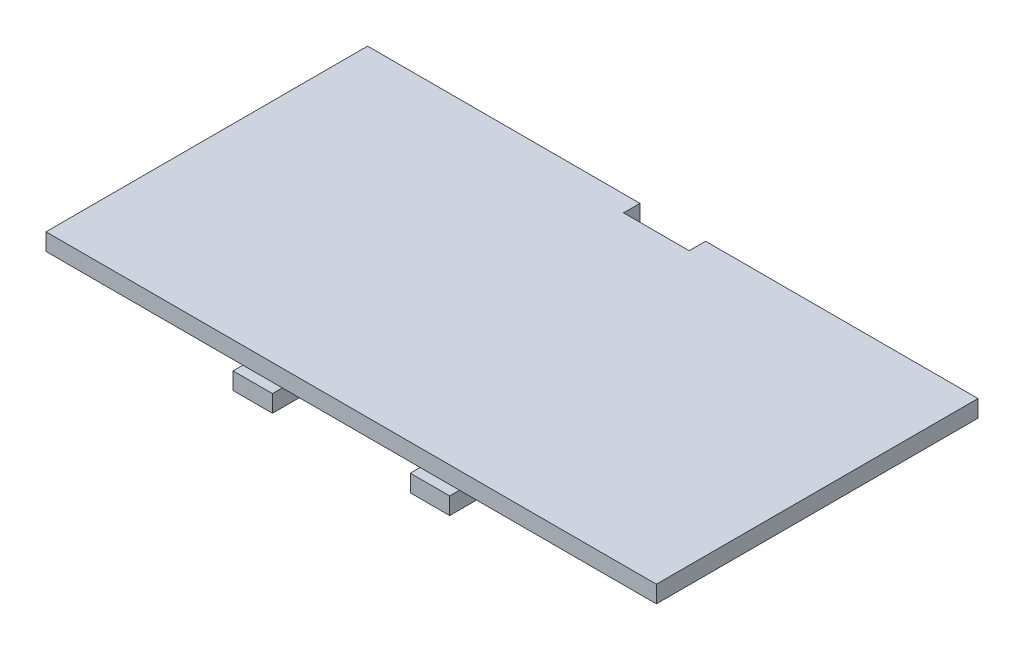
SolidWorks part; units mm, degrees
ref_plane "Front" through (0, 0, 0) normal (0, 0, 1) x (1, 0, 0)
ref_plane "Top" through (0, 0, 0) normal (0, 1, 0) x (1, 0, 0)
ref_plane "Right" through (0, 0, 0) normal (1, 0, 0) x (0, 0, -1)
sketch "Sketch1" plane through (0, 0, 0) normal (0, 1, 0) x (1, 0, 0)
  line L1 (-46.5, -24.5) -> (46.5, -24.5)
  line L2 (-46.5, -24.5) -> (-46.5, 24.5)
  line L3 (-46.5, 24.5) -> (46.5, 24.5)
  line L4 (46.5, -24.5) -> (46.5, 24.5)
  line L5 (-46.5, -24.5) -> (46.5, 24.5) construction
  line L6 (-46.5, 24.5) -> (46.5, -24.5) construction
  point P0 (0, 0)
  dimension "D1" = 49
  dimension "D2" = 93
extrude "Boss-Extrude1" add sketch "Sketch1" along normal blind 2.6
sketch "Sketch2" plane through (0, 2.6, 0) normal (0, 1, 0) x (1, 0, 0)
  line L0 (46.5, 24.5) -> (-46.5, 24.5) construction
  line L1 (-5, 24.5) -> (5, 24.5)
  line L2 (-5, 24.5) -> (-5, 22)
  line L3 (-5, 22) -> (5, 22)
  line L4 (5, 24.5) -> (5, 22)
  line L5 (-5, 24.5) -> (5, 22) construction
  line L6 (-5, 22) -> (5, 24.5) construction
  line L7 (0, 0) -> (0, 23.25) construction
  point P4 (0, 23.25)
  dimension "D1" = 2.5
  dimension "D2" = 10
extrude "Cut-Extrude1" cut sketch "Sketch2" against normal blind 2.6
sketch "Sketch3" plane through (0, 0, 0) normal (0, -1, 0) x (1, 0, 0)
  line L0 (-46.5, 24.5) -> (46.5, 24.5) construction
  line L1 (-16.5, 23) -> (-10.5, 23) construction
  line L2 (-16.5, 23) -> (-16.5, 26)
  line L3 (-16.5, 26) -> (-10.5, 26)
  line L4 (-10.5, 23) -> (-10.5, 26)
  line L5 (-16.5, 23) -> (-10.5, 26) construction
  line L6 (-16.5, 26) -> (-10.5, 23) construction
  line L7 (10.5, 23) -> (16.5, 23) construction
  line L8 (10.5, 23) -> (10.5, 26)
  line L9 (10.5, 26) -> (16.5, 26)
  line L10 (16.5, 23) -> (16.5, 26)
  line L11 (10.5, 23) -> (16.5, 26) construction
  line L12 (10.5, 26) -> (16.5, 23) construction
  line L13 (-46.5, -24.5) -> (-46.5, 24.5) construction
  line L14 (46.5, 24.5) -> (46.5, -24.5) construction
  line L15 (-16.5, 23) -> (-16.5, 21.5)
  line L16 (-16.5, 21.5) -> (-10.5, 21.5)
  line L17 (-10.5, 21.5) -> (-10.5, 23)
  line L18 (10.5, 23) -> (10.5, 21.5)
  line L19 (10.5, 21.5) -> (16.5, 21.5)
  line L20 (16.5, 21.5) -> (16.5, 23)
  point P4 (-13.5, 24.5)
  point P9 (13.5, 24.5)
  dimension "D1" = 6
  dimension "D2" = 6
  dimension "D3" = 3
  dimension "D4" = 3
  dimension "D5" = 30
  dimension "D6" = 30
  dimension "D7" = 1.5
  dimension "D8" = 1.5
extrude "Boss-Extrude2" add sketch "Sketch3" along normal blind 2.6
